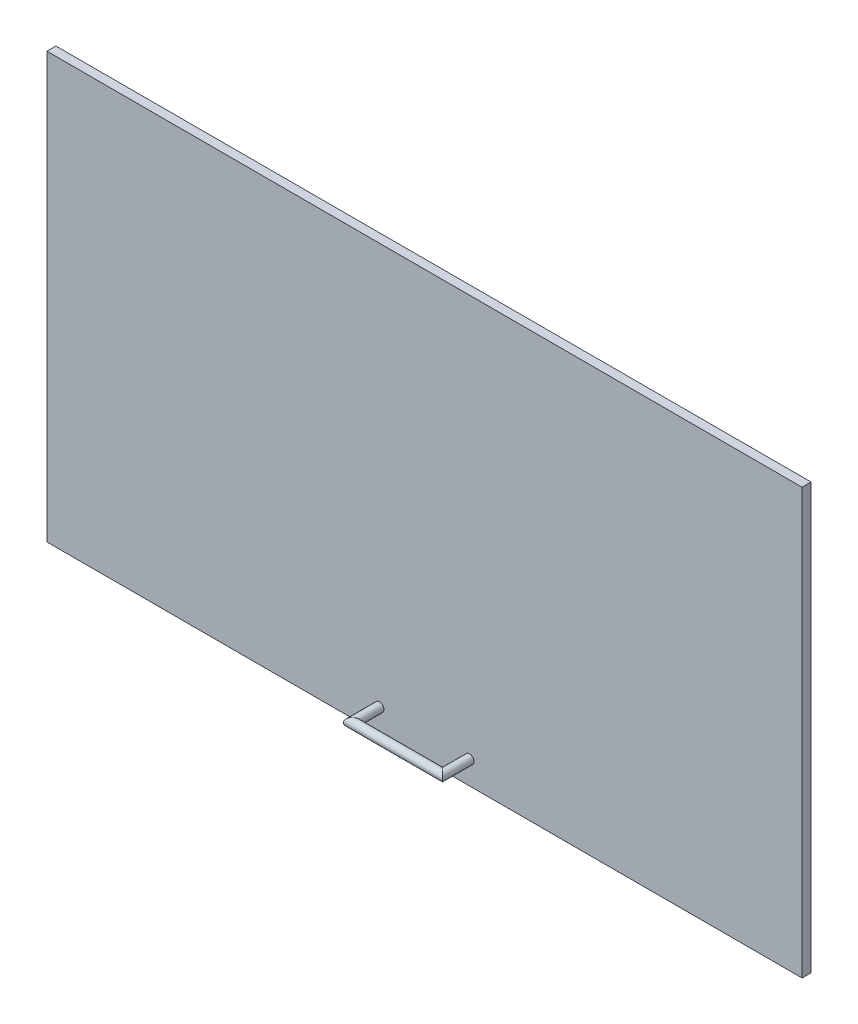
SolidWorks part; units mm, degrees
ref_plane "Front Plane" through (0, 0, 0) normal (0, 0, 1) x (1, 0, 0)
ref_plane "Top Plane" through (0, 0, 0) normal (0, 1, 0) x (1, 0, 0)
ref_plane "Right Plane" through (0, 0, 0) normal (1, 0, 0) x (0, 0, -1)
sketch "Sketch1" plane through (0, 0, 0) normal (0, 0, 1) x (1, 0, 0)
  line L1 (-419.24, -235.955) -> (419.24, -235.955)
  line L2 (-419.24, -235.955) -> (-419.24, 235.955)
  line L3 (-419.24, 235.955) -> (419.24, 235.955)
  line L4 (419.24, -235.955) -> (419.24, 235.955)
  line L5 (-419.24, -235.955) -> (419.24, 235.955) construction
  line L6 (-419.24, 235.955) -> (419.24, -235.955) construction
  point P0 (0, 0)
  dimension "D1" = 471.91
  dimension "D2" = 838.48
extrude "Boss-Extrude1" add sketch "Sketch1" along normal blind 10
sketch "Sketch2" plane through (0, 0, 10) normal (0, 0, 1) x (1, 0, 0)
  line L0 (0, 0) -> (0, -210) construction
  line L1 (-50, -210) -> (50, -210) construction
  circle A0 centre (50, -210) radius 5
  point P6 (0, -210)
  dimension "D2" = 10
  dimension "D1" = 210
  dimension "D3" = 100
sketch3d "3DSketch1"
  line L0 (-50, -210, 10) -> (-50, -210, 40)
  line L1 (50, -210, 10) -> (50, -210, 40)
  line L2 (50, -210, 40) -> (-50, -210, 40)
  point P7 (0, 0, 0)
  dimension "D1" = 30
sweep "Sweep3" add profiles "Sketch2" path "3DSketch1"
